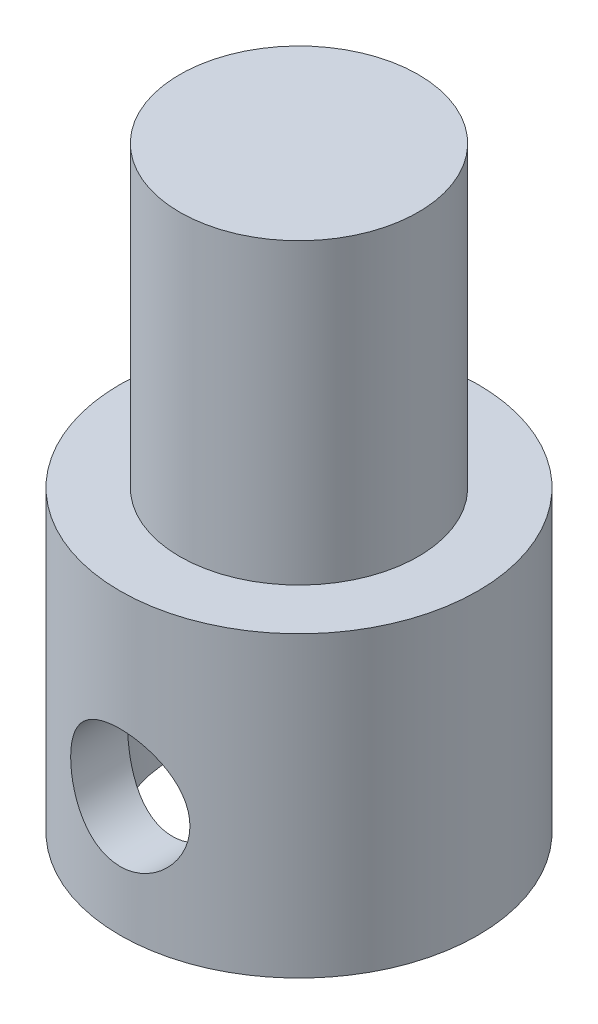
SolidWorks part; units mm, degrees
ref_plane "Alzado" through (0, 0, 0) normal (0, 0, 1) x (1, 0, 0)
ref_plane "Planta" through (0, 0, 0) normal (0, 1, 0) x (1, 0, 0)
ref_plane "Vista lateral" through (0, 0, 0) normal (1, 0, 0) x (0, 0, -1)
sketch "Croquis1" plane through (0, 0, 0) normal (0, 1, 0) x (1, 0, 0)
  circle A0 centre (0, 0) radius 6
  dimension "D1" = 12
extrude "Saliente-Extruir1" add sketch "Croquis1" along normal blind 10
sketch "Croquis2" plane through (0, 10, 0) normal (0, 1, 0) x (1, 0, 0)
  circle A0 centre (0, 0) radius 4
  dimension "D1" = 8
extrude "Saliente-Extruir2" add sketch "Croquis2" along normal blind 10
sketch "Croquis3" plane through (0, 0, 0) normal (0, -1, 0) x (1, 0, 0)
  circle A0 centre (0, 0) radius 4.25
  dimension "D1" = 8.5
extrude "Cortar-Extruir1" cut sketch "Croquis3" against normal blind 8
sketch "Croquis4" plane through (0, 0, 0) normal (0, 0, 1) x (1, 0, 0)
  line L0 (0, 0) -> (0, 4) construction
  circle A0 centre (0, 4) radius 2
  dimension "D1" = 4
  dimension "D2" = 4
extrude "Cortar-Extruir2" cut sketch "Croquis4" against normal through all and the other way through all
